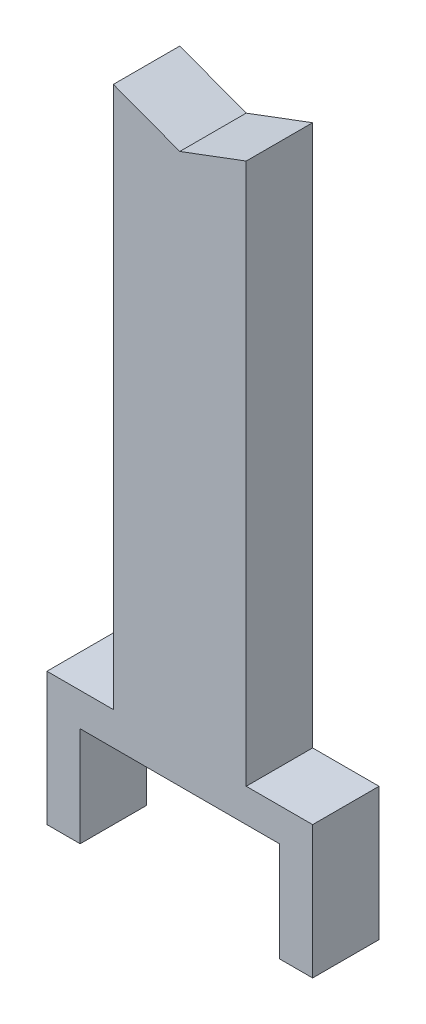
SolidWorks part; units mm, degrees
ref_plane "Front Plane" through (0, 0, 0) normal (0, 0, 1) x (1, 0, 0)
ref_plane "Top Plane" through (0, 0, 0) normal (0, 1, 0) x (1, 0, 0)
ref_plane "Right Plane" through (0, 0, 0) normal (1, 0, 0) x (0, 0, -1)
sketch "Sketch1" plane through (0, 0, 0) normal (0, 0, 1) x (1, 0, 0)
  line L0 (-50.8, 515.747) -> (0, 496.697)
  line L2 (-50.8, 101.6) -> (-50.8, 515.747)
  line L4 (50.8, 101.6) -> (50.8, 515.747)
  line L5 (0, 496.697) -> (50.8, 515.747)
  line L6 (0, 496.697) -> (0, 0) construction
  line L11 (-76.2, 0) -> (-76.2, 76.2)
  line L12 (-76.2, 76.2) -> (0, 76.2)
  line L13 (-76.2, 0) -> (-101.6, 0)
  line L14 (-101.6, 0) -> (-101.6, 101.6)
  line L15 (-101.6, 101.6) -> (-50.8, 101.6)
  line L17 (101.6, 101.6) -> (50.8, 101.6)
  line L18 (101.6, 0) -> (101.6, 101.6)
  line L19 (76.2, 0) -> (101.6, 0)
  line L20 (76.2, 0) -> (76.2, 76.2)
  line L21 (76.2, 76.2) -> (0, 76.2)
  point P0 (-76.2, 38.1)
  point P3 (0, 0)
  dimension "D1" = 203.2
  dimension "D2" = 101.6
  dimension "D3" = 19.05
  dimension "D4" = 101.6
  dimension "D5" = 25.4
  dimension "D6" = 25.4
  dimension "D7" = 515.747
extrude "Boss-Extrude1" add sketch "Sketch1" along normal mid plane 50.8
